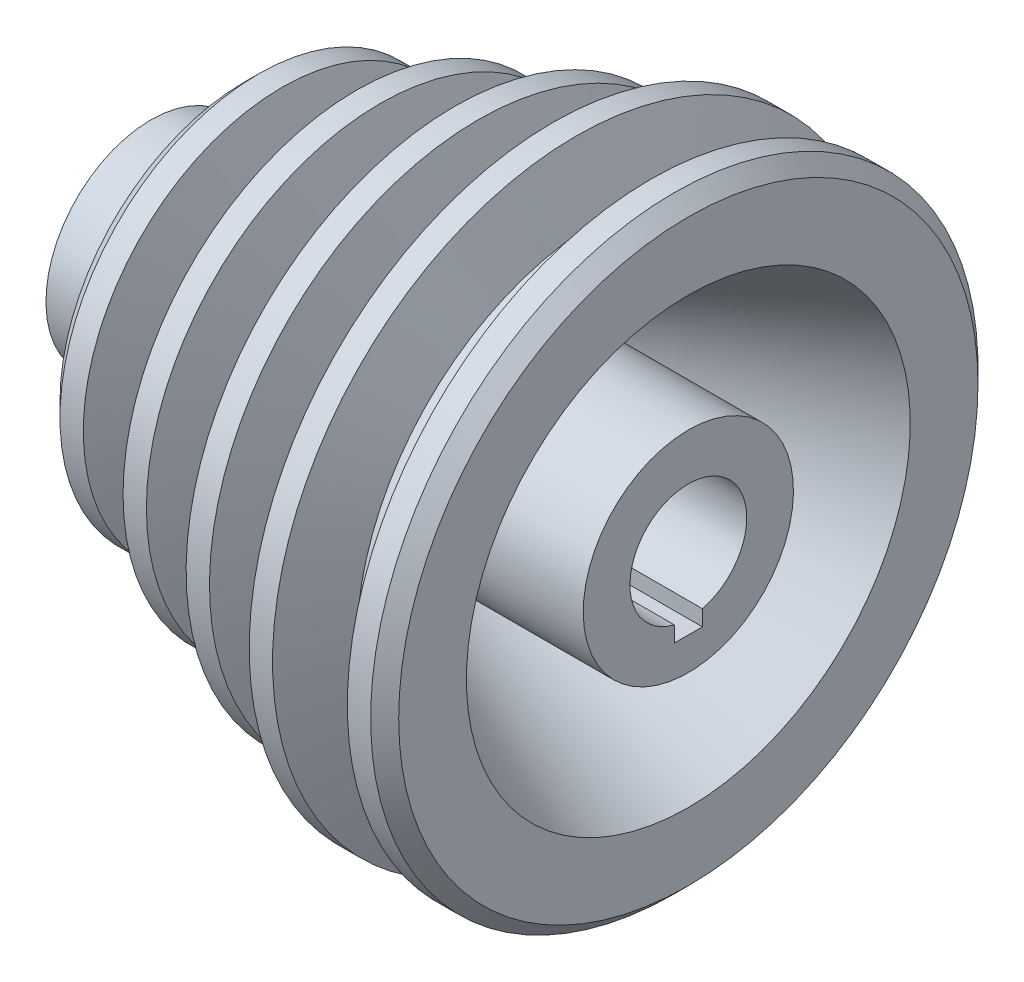
SolidWorks part; units mm, degrees
material "Titanium"
ref_plane "Front Plane" through (0, 0, 0) normal (0, 0, 1) x (1, 0, 0)
ref_plane "Top Plane" through (0, 0, 0) normal (0, 1, 0) x (1, 0, 0)
ref_plane "Right Plane" through (0, 0, 0) normal (1, 0, 0) x (0, 0, -1)
sketch "Sketch1" plane through (0, 0, 0) normal (0, 0, 1) x (1, 0, 0)
  line L0 (57.5, 0) -> (-57.5, 0) construction
  line L1 (57.5, 12.5) -> (-57.5, 12.5)
  line L2 (-57.5, 12.5) -> (-57.5, 22.5)
  line L3 (-57.5, 22.5) -> (-37.5, 22.5)
  line L4 (-37.5, 22.5) -> (-37.5, 42.5)
  line L5 (-37.5, 42.5) -> (-29.5, 42.5)
  line L6 (-29.5, 42.5) -> (-24, 27.5)
  line L7 (-24, 27.5) -> (-19, 27.5)
  line L8 (-19, 27.5) -> (-13.5, 50)
  line L9 (-13.5, 50) -> (-8.5, 50)
  line L10 (-8.5, 50) -> (-3, 35)
  line L11 (-3, 35) -> (2, 35)
  line L12 (2, 35) -> (7.5, 57.5)
  line L13 (7.5, 57.5) -> (12.5, 57.5)
  line L14 (12.5, 57.5) -> (18, 42.5)
  line L15 (18, 42.5) -> (23, 42.5)
  line L16 (23, 42.5) -> (28.5, 65)
  line L17 (28.5, 65) -> (33.5, 65)
  line L18 (33.5, 65) -> (39, 52.5)
  line L19 (39, 52.5) -> (44, 52.5)
  line L20 (44, 52.5) -> (49.5, 65)
  line L21 (49.5, 65) -> (57.5, 65)
  line L22 (57.5, 65) -> (57.5, 47.5)
  line L23 (57.5, 47.5) -> (12.5, 27.5)
  line L24 (12.5, 27.5) -> (12.5, 22.5)
  line L25 (12.5, 22.5) -> (57.5, 22.5)
  line L26 (57.5, 22.5) -> (57.5, 12.5)
  point P3 (0, 0)
  point P18 (18.7003, 27.3514)
  point P31 (19.0544, 32.8746)
  point P32 (31.6422, 39.4254)
  point P33 (8.7787, 29.9204)
  point P34 (60.1575, 34.5444)
  point P35 (0, 0)
  point P36 (51.9369, 63.8304)
  point P37 (0, 0)
  point P38 (0, 0)
  point P39 (5.439, 55.8667)
  point P40 (8.7787, 42.2513)
  point P41 (4.7571, 20.9128)
  point P42 (-37.5, 32.5)
  point P43 (-26.8494, 27.5)
  point P44 (-24.473, 27.5)
  point P45 (-28.0375, 27.5)
  point P46 (-15.5089, 35)
  point P47 (-2.022, 35)
  point P48 (-8.903, 50)
  point P49 (-5.7378, 35)
  point P50 (11.2404, 57.5)
  point P51 (-20.3365, 27.5)
  point P52 (-13.5, 50)
  point P53 (-11.7453, 50)
  point P54 (12.5, 27.5)
  point P55 (12.5, 35)
  point P56 (12.5, 30.5638)
  point P57 (0, 0)
  dimension "D1" = 115
  dimension "D2" = 25
  dimension "D3" = 130
  dimension "D4" = 8
  dimension "D5" = 8
  dimension "D6" = 45
  dimension "D7" = 100
  dimension "D8" = 115
  dimension "D9" = 85
  dimension "D10" = 45
  dimension "D11" = 95
  dimension "D12" = 52.5
  dimension "D13" = 16
  dimension "D14" = 5
  dimension "D15" = 42.5
  dimension "D16" = 35
  dimension "D17" = 27.5
  dimension "D18" = 20
  dimension "D19" = 16
  dimension "D20" = 16
  dimension "D21" = 13.5
  dimension "D22" = 16
  dimension "D23" = 16
revolve "Revolve1" add sketch "Sketch1" angle 360 about L0
chamfer "Chamfer1" distance 3 angle 45 2 edges at (57.5, 65, 0) (-37.5, 42.5, 0)
sketch "Sketch2" plane through (-57.5, 0, 0) normal (-1, 0, 0) x (0, 0, 1)
  line L1 (-3, -9.5) -> (3, -9.5)
  line L2 (-3, -9.5) -> (-3, -15.5)
  line L3 (-3, -15.5) -> (3, -15.5)
  line L4 (3, -9.5) -> (3, -15.5)
  line L5 (-3, -9.5) -> (3, -15.5) construction
  line L6 (-3, -15.5) -> (3, -9.5) construction
  circle A0 centre (0, 0) radius 12.5 construction
  point P0 (0, -12.5)
  point P7 (0, 0)
  dimension "D1" = 6
  dimension "D2" = 3
extrude "Cut-Extrude1" cut sketch "Sketch2" against normal through all
